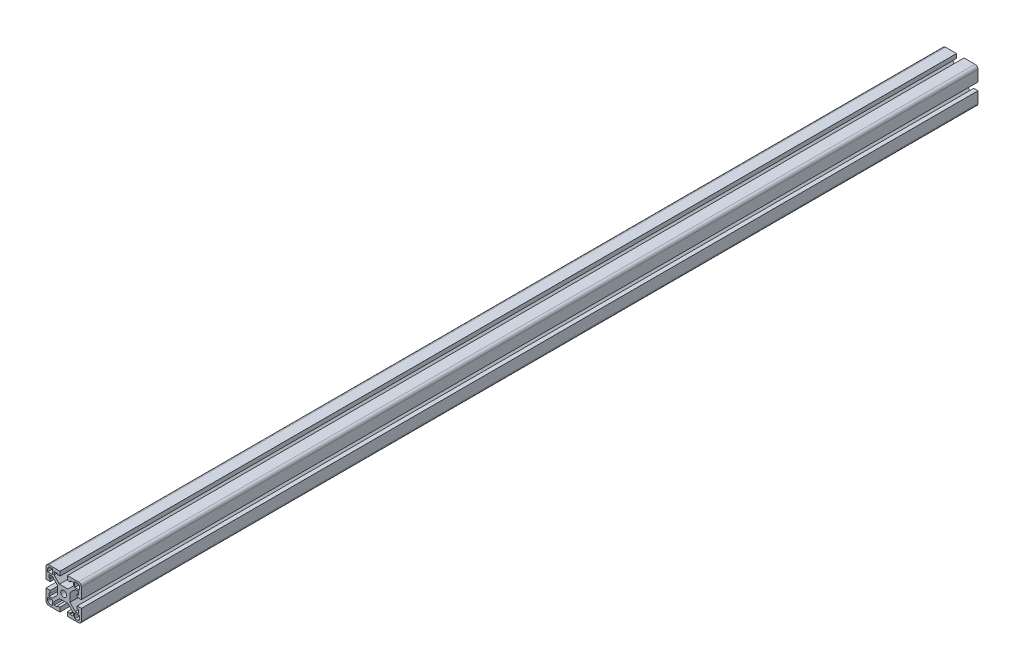
SolidWorks part; units mm, degrees
ref_plane "Front"
ref_plane "Top" through (0, 0, 0) normal (0, 1, 0) x (1, 0, 0)
ref_plane "Right" through (0, 0, 0) normal (1, 0, 0) x (0, 0, -1)
sketch "Sketch1" plane through (0, 0, 0) normal (0, 0, 1) x (1, 0, 0)
  line L0 (0, 0) -> (0, 30.3479) construction
  line L1 (0, 0) -> (-30.9616, 0) construction
  line L2 (-6.731, 0) -> (-6.731, 4.5757)
  line L3 (-6.731, 4.5757) -> (-12.4423, 10.287)
  line L4 (-15.6718, 10.287) -> (-15.6718, 6.858)
  line L5 (4.5757, 6.731) -> (10.287, 12.4423)
  line L6 (-19.05, 4.064) -> (-19.05, 15.875)
  line L7 (0, 6.731) -> (-4.5757, 6.731)
  line L8 (-4.5757, 6.731) -> (-10.287, 12.4423)
  line L9 (-10.287, 15.6718) -> (-6.858, 15.6718)
  line L10 (4.064, 19.05) -> (15.875, 19.05)
  line L11 (-4.064, 19.05) -> (-15.875, 19.05)
  line L12 (19.05, 4.064) -> (19.05, 15.875)
  line L13 (6.731, 4.5757) -> (12.4423, 10.287)
  line L14 (17.272, 11.8872) -> (17.272, 14.478)
  line L15 (11.8872, 17.272) -> (14.478, 17.272)
  line L16 (6.731, 0) -> (6.731, 4.5757)
  line L17 (6.731, 0) -> (6.731, -4.5757)
  line L18 (6.858, 15.6718) -> (6.858, 14.478)
  line L19 (4.064, 14.478) -> (6.858, 14.478)
  line L20 (10.287, -12.4423) -> (10.287, -15.6718)
  line L21 (12.4423, -10.287) -> (15.6718, -10.287)
  line L22 (19.05, -4.064) -> (19.05, -15.875)
  line L23 (-4.064, -19.05) -> (-15.875, -19.05)
  line L24 (4.064, -19.05) -> (15.875, -19.05)
  line L25 (11.8872, -11.8872) -> (17.272, -11.8872)
  line L26 (-17.272, -11.8872) -> (-17.272, -14.478)
  line L27 (-11.8872, -17.272) -> (-14.478, -17.272)
  line L28 (-19.05, -4.064) -> (-19.05, -15.875)
  line L29 (-11.8872, -11.8872) -> (-11.8872, -17.272)
  line L30 (-11.8872, -11.8872) -> (-17.272, -11.8872)
  line L31 (11.8872, -11.8872) -> (11.8872, -17.272)
  line L32 (-6.731, 0) -> (-6.731, -4.5757)
  line L33 (0, 6.731) -> (4.5757, 6.731)
  line L34 (-4.064, 19.05) -> (-4.064, 14.478)
  line L35 (4.064, 19.05) -> (4.064, 14.478)
  line L36 (-14.478, 4.064) -> (-19.05, 4.064)
  line L37 (14.478, 4.064) -> (14.478, 6.858)
  line L38 (15.6718, 6.858) -> (14.478, 6.858)
  line L39 (14.478, 4.064) -> (19.05, 4.064)
  line L40 (10.287, 15.6718) -> (6.858, 15.6718)
  line L41 (15.6718, 10.287) -> (15.6718, 6.858)
  line L42 (-10.287, 12.4423) -> (-10.287, 15.6718)
  line L43 (-12.4423, 10.287) -> (-15.6718, 10.287)
  line L44 (11.8872, 11.8872) -> (11.8872, 17.272)
  line L45 (-11.8872, 11.8872) -> (-17.272, 11.8872)
  line L46 (-11.8872, 11.8872) -> (-11.8872, 17.272)
  line L47 (-11.8872, 17.272) -> (-14.478, 17.272)
  line L48 (-17.272, 11.8872) -> (-17.272, 14.478)
  line L49 (11.8872, 11.8872) -> (17.272, 11.8872)
  line L50 (12.4423, 10.287) -> (15.6718, 10.287)
  line L51 (10.287, 12.4423) -> (10.287, 15.6718)
  line L52 (-10.287, -15.6718) -> (-6.858, -15.6718)
  line L53 (10.287, -15.6718) -> (6.858, -15.6718)
  line L54 (-12.4423, -10.287) -> (-15.6718, -10.287)
  line L55 (-10.287, -12.4423) -> (-10.287, -15.6718)
  line L56 (0, -6.731) -> (4.5757, -6.731)
  line L57 (11.8872, -17.272) -> (14.478, -17.272)
  line L58 (17.272, -11.8872) -> (17.272, -14.478)
  line L59 (6.731, -4.5757) -> (12.4423, -10.287)
  line L60 (15.6718, -10.287) -> (15.6718, -6.858)
  line L61 (-4.5757, -6.731) -> (-10.287, -12.4423)
  line L62 (0, -6.731) -> (-4.5757, -6.731)
  line L63 (4.5757, -6.731) -> (10.287, -12.4423)
  line L64 (14.478, -4.064) -> (19.05, -4.064)
  line L65 (-6.731, -4.5757) -> (-12.4423, -10.287)
  line L66 (15.6718, -6.858) -> (14.478, -6.858)
  line L67 (14.478, -4.064) -> (14.478, -6.858)
  line L68 (4.064, -19.05) -> (4.064, -14.478)
  line L69 (-4.064, 14.478) -> (-6.858, 14.478)
  line L70 (-6.858, 15.6718) -> (-6.858, 14.478)
  line L71 (4.064, -14.478) -> (6.858, -14.478)
  line L72 (6.858, -15.6718) -> (6.858, -14.478)
  line L73 (-15.6718, 6.858) -> (-14.478, 6.858)
  line L74 (-14.478, 4.064) -> (-14.478, 6.858)
  line L75 (-6.858, -15.6718) -> (-6.858, -14.478)
  line L76 (-4.064, -14.478) -> (-6.858, -14.478)
  line L77 (-4.064, -19.05) -> (-4.064, -14.478)
  line L78 (-14.478, -4.064) -> (-14.478, -6.858)
  line L79 (-15.6718, -6.858) -> (-14.478, -6.858)
  line L80 (-14.478, -4.064) -> (-19.05, -4.064)
  line L81 (-15.6718, -10.287) -> (-15.6718, -6.858)
  arc A0 (-15.875, 19.05) -> (-19.05, 15.875) centre (-15.875, 15.875) ccw
  arc A1 (-14.478, 17.272) -> (-17.272, 14.478) centre (-14.478, 14.478) ccw
  arc A2 (14.478, 17.272) -> (17.272, 14.478) centre (14.478, 14.478) cw
  arc A3 (-14.478, -17.272) -> (-17.272, -14.478) centre (-14.478, -14.478) cw
  arc A4 (14.478, -17.272) -> (17.272, -14.478) centre (14.478, -14.478) ccw
  arc A5 (15.875, 19.05) -> (19.05, 15.875) centre (15.875, 15.875) cw
  arc A6 (15.875, -19.05) -> (19.05, -15.875) centre (15.875, -15.875) ccw
  arc A7 (-15.875, -19.05) -> (-19.05, -15.875) centre (-15.875, -15.875) cw
  circle A8 centre (0, 0) radius 3.2639
  dimension "D2" = 3.175
  dimension "D5" = 19.05
  dimension "D6" = 3.048
  dimension "D13" = 10.287
  dimension "D15" = 5.3848
  dimension "D3" = 19.05
  dimension "D4" = 6.5278
  dimension "D14" = 2.794
  dimension "D1" = 45
  dimension "D7" = 8.9408
  dimension "D8" = 8.9408
  dimension "D9" = 12.319
  dimension "D10" = 12.319
  dimension "D11" = 14.986
  dimension "D12" = 14.986
  dimension "D16" = 7.1628
  dimension "D17" = 7.1628
  dimension "D18" = 7.747
  dimension "D19" = 6.858
  dimension "D20" = 7.747
  dimension "D21" = 6.858
  dimension "D22" = 19.05
extrude "FinalCut" add sketch "Sketch1" against normal blind 965.2
ref_plane "A" through (0, 0, 0) normal (0, 0, 1) x (1, 0, 0)
ref_plane "B" through (0, 0, -965.2) normal (0, 0, -1) x (-1, 0, 0)
ref_plane "Y+" through (0, 19.05, 0) normal (0, 1, 0) x (-1, 0, 0)
ref_plane "X+" through (19.05, 0, 0) normal (1, 0, 0) x (0, 0, -1)
ref_plane "Y-" through (0, -19.05, 0) normal (0, -1, 0) x (1, 0, 0)
ref_plane "X-" through (-19.05, 0, 0) normal (-1, 0, 0) x (0, 0, 1)
ref_plane "SLOT-1-3-" through (0, 0, 0) normal (1, 0, 0) x (0, 0, -1)
ref_plane "SLOT-2-4-" through (0, 0, 0) normal (0, 1, 0) x (-1, 0, 0)
sketch "Sketch38" plane through (0, 0, -965.2) normal (0, 0, -1) x (-1, 0, 0)
  point P0 (0, 0)
sketch "Sketch3" plane through (0, 19.05, 0) normal (0, 1, 0) x (-1, 0, 0)
  line L0 (4.064, 0) -> (15.875, 0) construction
  circle A0 centre (0, -21.717) radius 10.3124
  dimension "D1" = 20.6248
  dimension "D2" = 21.717
extrude "AFA1" [suppressed] cut sketch "Sketch3" against normal blind 16.51
sketch "Sketch5" plane through (19.05, 0, 0) normal (1, 0, 0) x (0, 0, -1)
  line L0 (0, 4.064) -> (0, 15.875) construction
  circle A0 centre (21.717, 0) radius 10.3124
  dimension "D1" = 20.6248
  dimension "D2" = 21.717
extrude "AFA2" [suppressed] cut sketch "Sketch5" against normal blind 16.51
sketch "Sketch6" plane through (0, -19.05, 0) normal (0, -1, 0) x (1, 0, 0)
  circle A0 centre (0, -21.717) radius 10.3124
  dimension "D1" = 21.717
  dimension "D2" = 20.6248
extrude "AFA3" [suppressed] cut sketch "Sketch6" against normal blind 16.51
sketch "Sketch8" plane through (-19.05, 0, 0) normal (-1, 0, 0) x (0, 0, 1)
  circle A0 centre (-21.717, 0) radius 10.3124
  dimension "D2" = 20.6248
  dimension "D1" = 21.717
extrude "AFA4" [suppressed] cut sketch "Sketch8" against normal blind 16.51
sketch "Sketch9" plane through (0, 19.05, 0) normal (0, 1, 0) x (-1, 0, 0)
  line L0 (-15.875, -965.2) -> (-4.064, -965.2) construction
  circle A0 centre (0, -943.483) radius 10.3124
  dimension "D2" = 20.6248
  dimension "D1" = 21.717
extrude "AFB1" [suppressed] cut sketch "Sketch9" against normal blind 16.51
sketch "Sketch12" plane through (19.05, 0, 0) normal (1, 0, 0) x (0, 0, -1)
  line L0 (965.2, 4.064) -> (965.2, 15.875) construction
  circle A0 centre (943.483, 0) radius 10.3124
  dimension "D2" = 20.6248
  dimension "D1" = 21.717
extrude "AFB2" [suppressed] cut sketch "Sketch12" against normal blind 16.51
sketch "Sketch13" plane through (0, -19.05, 0) normal (0, -1, 0) x (1, 0, 0)
  line L0 (-15.875, -965.2) -> (-4.064, -965.2) construction
  circle A0 centre (0, -943.483) radius 10.3124
  point P2 (-9.9695, -965.2)
  dimension "D3" = 20.6248
  dimension "D1" = 0
  dimension "D2" = 21.717
extrude "AFB3" [suppressed] cut sketch "Sketch13" against normal blind 16.51
sketch "Sketch14" plane through (-19.05, 0, 0) normal (-1, 0, 0) x (0, 0, 1)
  line L0 (-965.2, 15.875) -> (-965.2, 4.064) construction
  circle A0 centre (-943.483, 0) radius 10.3124
  dimension "D2" = 20.6248
  dimension "D1" = 21.717
extrude "AFB4" [suppressed] cut sketch "Sketch14" against normal blind 16.51
sketch "Sketch25" plane through (0, 19.05, 0) normal (0, 1, 0) x (-1, 0, 0)
  circle A0 centre (0, -18.3134) radius 10.3124
  dimension "D1" = 20.6248
  dimension "D2" = 18.3134
extrude "BFA1" [suppressed] cut sketch "Sketch25" against normal blind 16.51
sketch "Sketch27" plane through (19.05, 0, 0) normal (1, 0, 0) x (0, 0, -1)
  line L0 (0, 4.064) -> (0, 15.875) construction
  circle A0 centre (18.3134, 0) radius 10.3124
  dimension "D1" = 20.6248
  dimension "D2" = 18.3134
extrude "BFA2" [suppressed] cut sketch "Sketch27" against normal blind 16.51
sketch "Sketch24" plane through (0, -19.05, 0) normal (0, -1, 0) x (1, 0, 0)
  circle A0 centre (0, -18.3134) radius 10.3124
  dimension "D1" = 18.3134
  dimension "D2" = 20.6248
extrude "BFA3" [suppressed] cut sketch "Sketch24" against normal blind 16.51
sketch "Sketch23" plane through (-19.05, 0, 0) normal (-1, 0, 0) x (0, 0, 1)
  circle A0 centre (-18.3134, 0) radius 10.3124
  dimension "D1" = 18.3134
  dimension "D2" = 20.6248
extrude "BFA4" [suppressed] cut sketch "Sketch23" against normal blind 16.51
sketch "Sketch15" plane through (0, 19.05, 0) normal (0, 1, 0) x (-1, 0, 0)
  line L0 (-20.955, -965.2) -> (20.955, -965.2) construction
  circle A0 centre (0, -946.8866) radius 10.3124
  dimension "D2" = 20.6248
  dimension "D1" = 18.3134
extrude "BFB1" [suppressed] cut sketch "Sketch15" against normal blind 16.51
sketch "Sketch17" plane through (19.05, 0, 0) normal (1, 0, 0) x (0, 0, -1)
  line L0 (965.2, -20.955) -> (965.2, 20.955) construction
  circle A0 centre (946.8866, 0) radius 10.3124
  dimension "D2" = 20.6248
  dimension "D1" = 18.3134
extrude "BFB2" [suppressed] cut sketch "Sketch17" against normal blind 16.51
sketch "Sketch18" plane through (0, -19.05, 0) normal (0, -1, 0) x (1, 0, 0)
  line L0 (-20.955, -965.2) -> (20.955, -965.2) construction
  circle A0 centre (0, -946.8866) radius 10.3124
  dimension "D2" = 20.6248
  dimension "D1" = 18.3134
extrude "BFB3" [suppressed] cut sketch "Sketch18" against normal blind 16.51
sketch "Sketch19" plane through (-19.05, 0, 0) normal (-1, 0, 0) x (0, 0, 1)
  line L0 (-965.2, 20.955) -> (-965.2, -20.955) construction
  circle A0 centre (-946.8866, 0) radius 10.3124
  dimension "D2" = 20.6248
  dimension "D1" = 18.3134
extrude "BFB4" [suppressed] cut sketch "Sketch19" against normal blind 16.51
sketch "Sketch28" plane through (0, 0, 0) normal (0, 0, 1) x (1, 0, 0)
  circle A0 centre (0, 0) radius 3.81
  dimension "D1" = 7.62
extrude "TPA660015" [suppressed] cut sketch "Sketch28" against normal blind 25.4
sketch "Sketch29" plane through (0, 0, -965.2) normal (0, 0, -1) x (-1, 0, 0)
  circle A0 centre (0, 0) radius 3.81
  dimension "D1" = 7.62
extrude "TPB660015" [suppressed] cut sketch "Sketch29" against normal blind 25.4
sketch "Sketch30" plane through (0, 0, 0) normal (0, 0, 1) x (1, 0, 0)
  circle A0 centre (0, 0) radius 3.937
  dimension "D1" = 7.874
extrude "TPA660034" [suppressed] cut sketch "Sketch30" against normal blind 24.13
sketch "Sketch31" plane through (0, 0, -965.2) normal (0, 0, -1) x (-1, 0, 0)
  circle A0 centre (0, 0) radius 3.937
  dimension "D1" = 7.874
extrude "TPB660034" [suppressed] cut sketch "Sketch31" against normal blind 24.13
sketch "Sketch32" plane through (0, 0, 0) normal (0, 0, 1) x (1, 0, 0)
  circle A0 centre (0, 0) radius 4.064
  dimension "D1" = 8.128
extrude "TPA660033" [suppressed] cut sketch "Sketch32" against normal blind 22.86
sketch "Sketch33" plane through (0, 0, -965.2) normal (0, 0, -1) x (-1, 0, 0)
  circle A0 centre (0, 0) radius 4.064
  dimension "D1" = 8.128
extrude "TPB660033" [suppressed] cut sketch "Sketch33" against normal blind 22.86
sketch "Sketch34" plane through (0, 0, 0) normal (0, 0, 1) x (1, 0, 0)
  circle A0 centre (0, 0) radius 4.7625
  dimension "D1" = 9.525
extrude "TPA660009" [suppressed] cut sketch "Sketch34" against normal blind 21.59
sketch "Sketch35" plane through (0, 0, -965.2) normal (0, 0, -1) x (-1, 0, 0)
  circle A0 centre (0, 0) radius 4.7625
  dimension "D1" = 9.525
extrude "TPB660009" [suppressed] cut sketch "Sketch35" against normal blind 21.59
sketch "Sketch36" plane through (0, 0, 0) normal (0, 0, 1) x (1, 0, 0)
  circle A0 centre (0, 0) radius 5.5626
  dimension "D1" = 11.1252
extrude "TPA660030" [suppressed] cut sketch "Sketch36" against normal blind 20.32
sketch "Sketch37" plane through (0, 0, -965.2) normal (0, 0, -1) x (-1, 0, 0)
  circle A0 centre (0, 0) radius 5.5626
  dimension "D1" = 11.1252
extrude "TPB660030" [suppressed] cut sketch "Sketch37" against normal blind 20.32
sketch "Sketch39" plane through (0, 0, 0) normal (1, 0, 0) x (0, 0, -1)
  line L0 (0, 19.05) -> (38.1, -19.05)
  line L1 (965.2, 19.05) -> (0, 19.05) construction
  line L2 (965.2, -19.05) -> (0, -19.05) construction
  dimension "D1" = 45
extrude "MITA1" [suppressed] cut sketch "Sketch39" against normal through all and the other way through all flip side to cut
ref_plane "AMITA1" [suppressed] through (0, 9.525, -9.525) normal (0, 0.7071, -0.7071) x (-1, 0, 0)
ref_plane "AMITOFFA1" [suppressed] through (0, 14.0151, -14.0151) normal (0, 0.7071, -0.7071) x (-1, 0, 0)
sketch "Sketch43" [suppressed] plane through (0, 14.0151, -14.0151) normal (0, 0.7071, -0.7071) x (-1, 0, 0)
  line L0 (4.064, 13.4704) -> (15.875, 13.4704) construction
  circle A0 centre (0, -15.1046) radius 9.525
  dimension "D2" = 19.05
  dimension "D1" = 28.575
extrude "MITCBA1" [suppressed] cut sketch "Sketch43" along normal through all
sketch "Sketch44" [suppressed] plane through (0, 14.0151, -14.0151) normal (0, 0.7071, -0.7071) x (-1, 0, 0)
  line L0 (4.064, 13.4704) -> (15.875, 13.4704) construction
  circle A0 centre (0, -15.1046) radius 4.1656
  dimension "D1" = 8.3312
  dimension "D2" = 28.575
extrude "MITDRA1" [suppressed] cut sketch "Sketch44" against normal through all
sketch "Sketch45" [suppressed] plane through (0, 14.0151, -14.0151) normal (0, 0.7071, -0.7071) x (-1, 0, 0)
  line L0 (-9.525, 13.4704) -> (-9.525, -4.0048)
  line L1 (9.525, -4.0048) -> (9.525, 13.4704)
  line L2 (9.525, 13.4704) -> (-9.525, 13.4704)
  line L3 (4.064, 13.4704) -> (15.875, 13.4704) construction
  arc A0 (-9.525, -4.0048) -> (9.525, -4.0048) centre (0, -4.0048) ccw
  dimension "D1" = 17.4752
  dimension "D2" = 9.525
extrude "MITEBA1" [suppressed] cut sketch "Sketch45" along normal through all
sketch "Sketch46" [suppressed] plane through (0, 14.0151, -14.0151) normal (0, 0.7071, -0.7071) x (-1, 0, 0)
  line L0 (-4.1656, 13.4704) -> (-4.1656, -4.0048)
  line L1 (4.1656, -4.0048) -> (4.1656, 13.4704)
  line L2 (4.1656, 13.4704) -> (-4.1656, 13.4704)
  line L3 (4.064, 13.4704) -> (15.875, 13.4704) construction
  arc A0 (-4.1656, -4.0048) -> (4.1656, -4.0048) centre (0, -4.0048) ccw
  dimension "D1" = 4.1656
  dimension "D2" = 17.4752
extrude "MITEDA1" [suppressed] cut sketch "Sketch46" against normal through all
sketch "Sketch40" plane through (0, 0, 0) normal (1, 0, 0) x (0, 0, -1)
  line L0 (965.2, 19.05) -> (927.1, -19.05)
  line L1 (965.2, 19.05) -> (0, 19.05) construction
  line L2 (965.2, -19.05) -> (0, -19.05) construction
  dimension "D1" = 45
extrude "MITB1" [suppressed] cut sketch "Sketch40" against normal through all and the other way through all
ref_plane "AMITB1" [suppressed] through (0, -41.275, -41.275) normal (0, 0.7071, 0.7071) x (1, 0, 0)
ref_plane "AMITOFFB1" [suppressed] through (0, -36.7849, -36.7849) normal (0, 0.7071, 0.7071) x (1, 0, 0)
sketch "Sketch47" [suppressed] plane through (0, -36.7849, -36.7849) normal (0, 0.7071, 0.7071) x (1, 0, 0)
  line L0 (15.875, 85.3124) -> (4.064, 85.3124) construction
  circle A0 centre (0, 56.7374) radius 9.525
  dimension "D1" = 28.575
  dimension "D2" = 19.05
extrude "MITCBB1" [suppressed] cut sketch "Sketch47" along normal through all
sketch "Sketch48" [suppressed] plane through (0, -36.7849, -36.7849) normal (0, 0.7071, 0.7071) x (1, 0, 0)
  line L0 (15.875, 85.3124) -> (4.064, 85.3124) construction
  circle A0 centre (0, 56.7374) radius 4.1656
  dimension "D1" = 28.575
  dimension "D2" = 8.3312
extrude "MITDRB1" [suppressed] cut sketch "Sketch48" against normal through all
sketch "Sketch49" [suppressed] plane through (0, -36.7849, -36.7849) normal (0, 0.7071, 0.7071) x (1, 0, 0)
  line L0 (-9.525, 67.8372) -> (-9.525, 85.3124)
  line L1 (-9.525, 85.3124) -> (9.525, 85.3124)
  line L2 (9.525, 85.3124) -> (9.525, 67.8372)
  line L3 (15.875, 85.3124) -> (4.064, 85.3124) construction
  arc A0 (9.525, 67.8372) -> (-9.525, 67.8372) centre (0, 67.8372) cw
  dimension "D2" = 9.525
  dimension "D1" = 17.4752
extrude "MITEBB1" [suppressed] cut sketch "Sketch49" along normal through all
sketch "Sketch50" [suppressed] plane through (0, -36.7849, -36.7849) normal (0, 0.7071, 0.7071) x (1, 0, 0)
  line L0 (-4.1656, 85.3124) -> (-4.1656, 67.8372)
  line L1 (4.1656, 67.8372) -> (4.1656, 85.3124)
  line L2 (4.1656, 85.3124) -> (-4.1656, 85.3124)
  line L3 (15.875, 85.3124) -> (4.064, 85.3124) construction
  arc A0 (-4.1656, 67.8372) -> (4.1656, 67.8372) centre (0, 67.8372) ccw
  dimension "D2" = 4.1656
  dimension "D1" = 17.4752
extrude "MITEDB1" [suppressed] cut sketch "Sketch50" against normal through all
sketch "Sketch41" plane through (0, 0, 0) normal (1, 0, 0) x (0, 0, -1)
  line L0 (0, -19.05) -> (38.1, 19.05)
  line L1 (965.2, -19.05) -> (0, -19.05) construction
  line L2 (965.2, 19.05) -> (0, 19.05) construction
  dimension "D1" = 45
extrude "MITA3" [suppressed] cut sketch "Sketch41" against normal through all and the other way through all
ref_plane "AMITA3" [suppressed] through (0, -9.525, -9.525) normal (0, -0.7071, -0.7071) x (-1, 0, 0)
ref_plane "AMITOFFA3" [suppressed] through (0, -14.0151, -14.0151) normal (0, -0.7071, -0.7071) x (-1, 0, 0)
sketch "Sketch51" [suppressed] plane through (0, -14.0151, -14.0151) normal (0, -0.7071, -0.7071) x (-1, 0, 0)
  line L0 (15.875, -13.4704) -> (4.064, -13.4704) construction
  circle A0 centre (0, 15.1046) radius 9.525
  dimension "D1" = 19.05
  dimension "D2" = 28.575
extrude "MITCBA3" [suppressed] cut sketch "Sketch51" along normal through all
sketch "Sketch52" [suppressed] plane through (0, -14.0151, -14.0151) normal (0, -0.7071, -0.7071) x (-1, 0, 0)
  line L0 (15.875, -13.4704) -> (4.064, -13.4704) construction
  circle A0 centre (0, 15.1046) radius 4.1656
  dimension "D1" = 28.575
  dimension "D2" = 8.3312
extrude "MITDRA3" [suppressed] cut sketch "Sketch52" against normal through all
sketch "Sketch53" [suppressed] plane through (0, -14.0151, -14.0151) normal (0, -0.7071, -0.7071) x (-1, 0, 0)
  line L0 (-9.525, -13.4704) -> (-9.525, 4.0048)
  line L1 (9.525, 4.0048) -> (9.525, -13.4704)
  line L2 (9.525, -13.4704) -> (-9.525, -13.4704)
  line L3 (15.875, -13.4704) -> (4.064, -13.4704) construction
  arc A0 (-9.525, 4.0048) -> (9.525, 4.0048) centre (0, 4.0048) cw
  dimension "D1" = 9.525
  dimension "D2" = 17.4752
extrude "MITEBA3" [suppressed] cut sketch "Sketch53" along normal through all
sketch "Sketch54" [suppressed] plane through (0, -14.0151, -14.0151) normal (0, -0.7071, -0.7071) x (-1, 0, 0)
  line L0 (-4.1656, -13.4704) -> (-4.1656, 4.0048)
  line L1 (4.1656, 4.0048) -> (4.1656, -13.4704)
  line L2 (4.1656, -13.4704) -> (-4.1656, -13.4704)
  line L3 (15.875, -13.4704) -> (4.064, -13.4704) construction
  arc A0 (-4.1656, 4.0048) -> (4.1656, 4.0048) centre (0, 4.0048) cw
  dimension "D1" = 4.1656
  dimension "D2" = 17.4752
extrude "MITEDA3" [suppressed] cut sketch "Sketch54" against normal through all
sketch "Sketch42" plane through (0, 0, 0) normal (1, 0, 0) x (0, 0, -1)
  line L0 (965.2, -19.05) -> (927.1, 19.05)
  line L1 (965.2, -19.05) -> (0, -19.05) construction
  line L2 (965.2, 19.05) -> (0, 19.05) construction
  dimension "D1" = 45
extrude "MITB3" [suppressed] cut sketch "Sketch42" against normal through all and the other way through all flip side to cut
ref_plane "AMITB3" [suppressed] through (0, 41.275, -41.275) normal (0, -0.7071, 0.7071) x (1, 0, 0)
ref_plane "AMITOFFB3" [suppressed] through (0, 36.7849, -36.7849) normal (0, -0.7071, 0.7071) x (1, 0, 0)
sketch "Sketch55" [suppressed] plane through (0, 36.7849, -36.7849) normal (0, -0.7071, 0.7071) x (1, 0, 0)
  line L0 (4.064, -85.3124) -> (15.875, -85.3124) construction
  circle A0 centre (0, -56.7374) radius 9.525
  dimension "D1" = 19.05
  dimension "D2" = 28.575
extrude "MITCBB3" [suppressed] cut sketch "Sketch55" along normal through all
sketch "Sketch56" [suppressed] plane through (0, 36.7849, -36.7849) normal (0, -0.7071, 0.7071) x (1, 0, 0)
  line L0 (4.064, -85.3124) -> (15.875, -85.3124) construction
  circle A0 centre (0, -56.7374) radius 4.1656
  dimension "D1" = 28.575
  dimension "D2" = 8.3312
extrude "MITDRB3" [suppressed] cut sketch "Sketch56" against normal through all
sketch "Sketch57" [suppressed] plane through (0, 36.7849, -36.7849) normal (0, -0.7071, 0.7071) x (1, 0, 0)
  line L0 (-9.525, -85.3124) -> (-9.525, -67.8372)
  line L1 (9.525, -67.8372) -> (9.525, -85.3124)
  line L2 (9.525, -85.3124) -> (-9.525, -85.3124)
  line L3 (4.064, -85.3124) -> (15.875, -85.3124) construction
  arc A0 (-9.525, -67.8372) -> (9.525, -67.8372) centre (0, -67.8372) cw
  dimension "D1" = 17.4752
  dimension "D2" = 9.525
extrude "MITEBB3" [suppressed] cut sketch "Sketch57" along normal through all
sketch "Sketch58" [suppressed] plane through (0, 36.7849, -36.7849) normal (0, -0.7071, 0.7071) x (1, 0, 0)
  line L0 (-4.1656, -85.3124) -> (-4.1656, -67.8372)
  line L1 (4.1656, -67.8372) -> (4.1656, -85.3124)
  line L2 (4.1656, -85.3124) -> (-4.1656, -85.3124)
  line L3 (4.064, -85.3124) -> (15.875, -85.3124) construction
  arc A0 (-4.1656, -67.8372) -> (4.1656, -67.8372) centre (0, -67.8372) cw
  dimension "D1" = 17.4752
  dimension "D2" = 4.1656
extrude "MITEDB3" [suppressed] cut sketch "Sketch58" against normal through all
